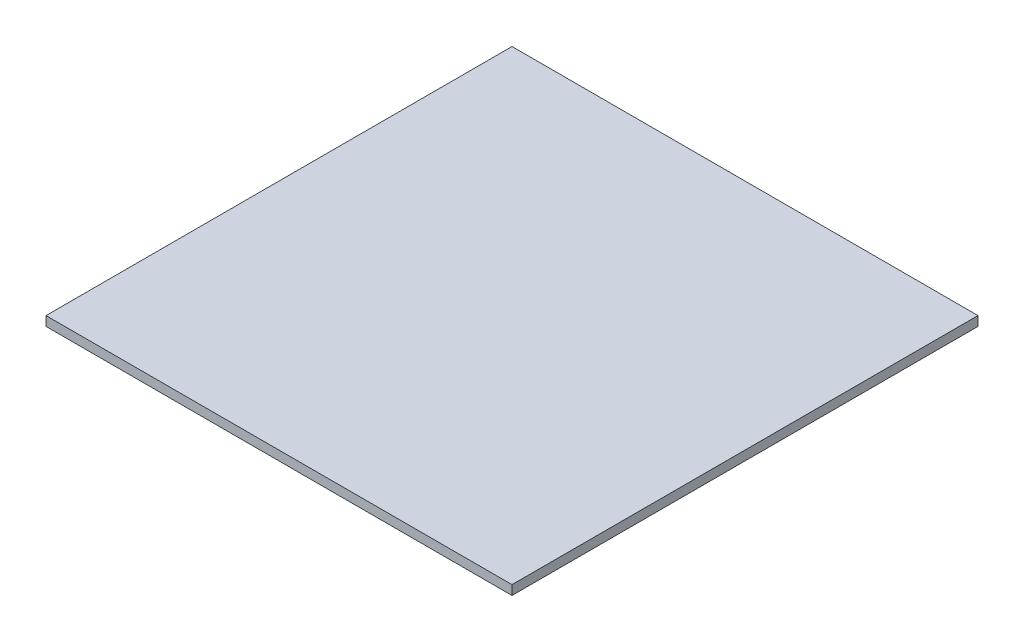
SolidWorks part; units mm, degrees
ref_plane "Front Plane" through (0, 0, 0) normal (0, 0, 1) x (1, 0, 0)
ref_plane "Top Plane" through (0, 0, 0) normal (0, 1, 0) x (1, 0, 0)
ref_plane "Right Plane" through (0, 0, 0) normal (1, 0, 0) x (0, 0, -1)
ref_plane "Plane1" through (0, 695.2, 0) normal (0, 1, 0) x (1, 0, 0)
sketch "Sketch2" plane through (0, 695.2, 0) normal (0, 1, 0) x (1, 0, 0)
  line L1 (104.5498, 495.3968) -> (1094.4932, 495.3968)
  line L2 (104.5498, 495.3968) -> (104.5498, -494.6032)
  line L3 (104.5498, -494.6032) -> (1094.4932, -494.6032)
  line L4 (1094.4932, 495.3968) -> (1094.4932, -494.6032)
extrude "Boss-Extrude1" add sketch "Sketch2" along normal blind 20
